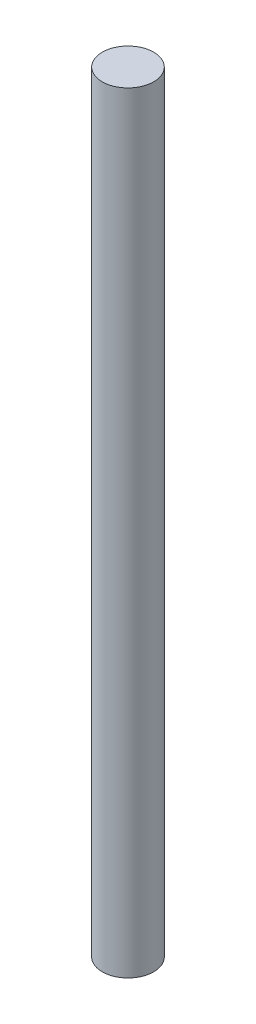
SolidWorks part; units mm, degrees
material "1060 Alloy"
ref_plane "Front Plane" through (0, 0, 0) normal (0, 0, 1) x (1, 0, 0)
ref_plane "Top Plane" through (0, 0, 0) normal (0, 1, 0) x (1, 0, 0)
ref_plane "Right Plane" through (0, 0, 0) normal (1, 0, 0) x (0, 0, -1)
sketch "Sketch1" plane through (0, 0, 0) normal (0, 1, 0) x (1, 0, 0)
  circle A0 centre (0, 0) radius 3.81
  dimension "D1" = 7.62
extrude "Boss-Extrude1" add sketch "Sketch1" along normal blind 114.3
